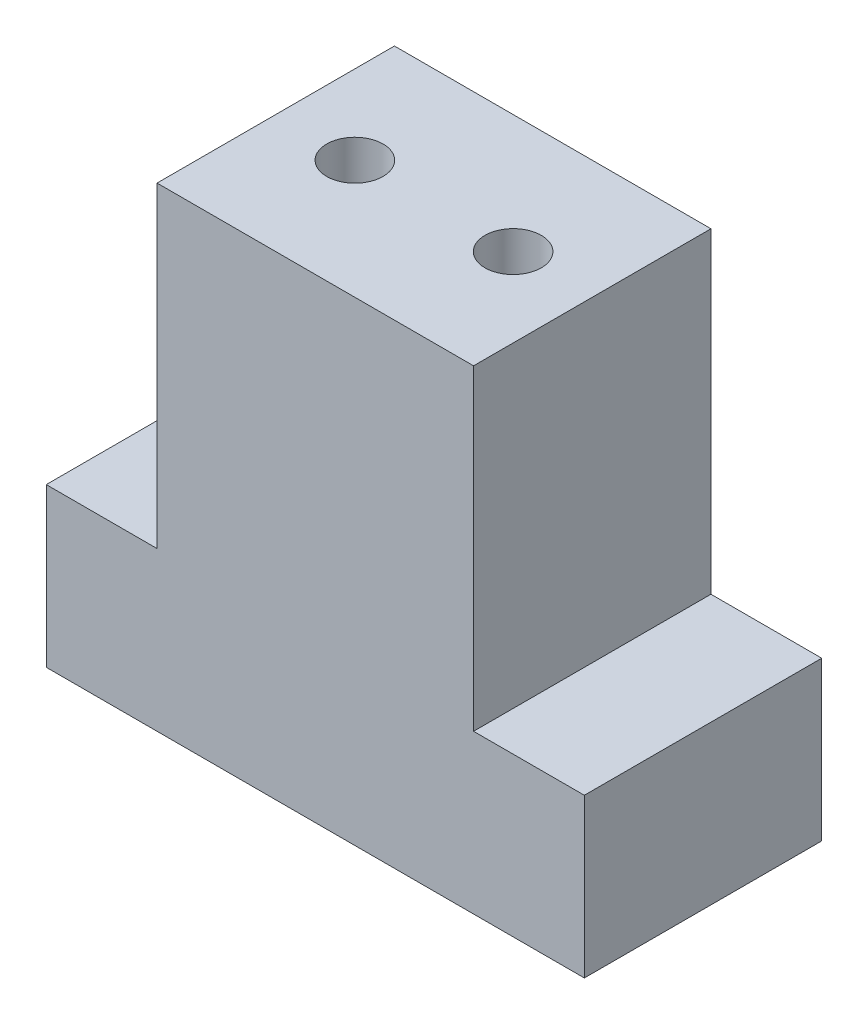
SolidWorks part; units mm, degrees
ref_plane "Front Plane" through (0, 0, 0) normal (0, 0, 1) x (1, 0, 0)
ref_plane "Top Plane" through (0, 0, 0) normal (0, 1, 0) x (1, 0, 0)
ref_plane "Right Plane" through (0, 0, 0) normal (1, 0, 0) x (0, 0, -1)
sketch "Sketch1" plane through (0, 0, 0) normal (0, 1, 0) x (1, 0, 0)
  line L1 (-6.35, -4.7625) -> (6.35, -4.7625)
  line L2 (-6.35, -4.7625) -> (-6.35, 4.7625)
  line L3 (-6.35, 4.7625) -> (6.35, 4.7625)
  line L4 (6.35, -4.7625) -> (6.35, 4.7625)
  line L5 (-6.35, -4.7625) -> (6.35, 4.7625) construction
  line L6 (-6.35, 4.7625) -> (6.35, -4.7625) construction
  point P0 (0, 0)
  dimension "D1" = 9.525
  dimension "D2" = 12.7
extrude "Boss-Extrude1" add sketch "Sketch1" along normal blind 12.7
sketch "Sketch2" plane through (0, 12.7, 0) normal (0, 1, 0) x (1, 0, 0)
  line L0 (3.175, 0) -> (-3.175, 0) construction
  circle A0 centre (-3.175, 0) radius 1.1303
  circle A1 centre (3.175, 0) radius 1.1303
  dimension "D2" = 2.2606
  dimension "D3" = 2.2606
  dimension "D1" = 6.35
extrude "Cut-Extrude1" cut sketch "Sketch2" against normal blind 6.35
sketch "Sketch3" plane through (0, 0, 0) normal (0, -1, 0) x (1, 0, 0)
  line L0 (-6.35, 4.7625) -> (6.35, 4.7625) construction
  line L1 (-10.795, -4.7625) -> (10.795, -4.7625)
  line L2 (-10.795, -4.7625) -> (-10.795, 4.7625)
  line L3 (-10.795, 4.7625) -> (10.795, 4.7625)
  line L4 (10.795, -4.7625) -> (10.795, 4.7625)
  line L5 (-10.795, -4.7625) -> (10.795, 4.7625) construction
  line L6 (-10.795, 4.7625) -> (10.795, -4.7625) construction
  point P0 (0, 0)
  dimension "D1" = 21.59
extrude "Boss-Extrude2" add sketch "Sketch3" along normal blind 6.35
sketch "Sketch4" plane through (0, -6.35, 0) normal (0, -1, 0) x (1, 0, 0)
  line L0 (-4.7625, 0) -> (4.7625, 0) construction
  circle A0 centre (-4.7625, 0) radius 1.1303
  circle A1 centre (4.7625, 0) radius 1.1303
  dimension "D2" = 2.2606
  dimension "D3" = 2.2606
  dimension "D1" = 9.525
extrude "Cut-Extrude2" cut sketch "Sketch4" against normal blind 6.35
